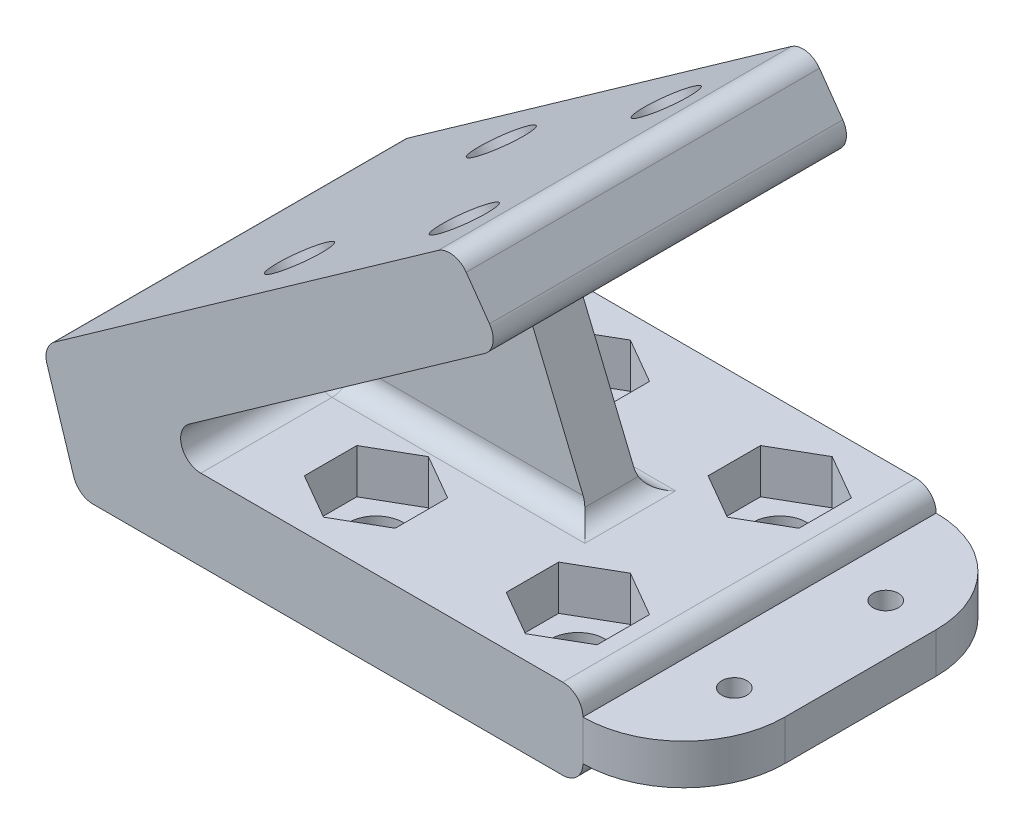
SolidWorks part; units mm, degrees
material "ABS"
ref_plane "Front Plane" through (0, 0, 0) normal (0, 0, 1) x (1, 0, 0)
ref_plane "Top Plane" through (0, 0, 0) normal (0, 1, 0) x (1, 0, 0)
ref_plane "Right Plane" through (0, 0, 0) normal (1, 0, 0) x (0, 0, -1)
sketch "Sketch1" plane through (0, 0, 0) normal (0, 0, 1) x (1, 0, 0)
  line L0 (0, 0) -> (63.5, 0)
  line L1 (63.5, 0) -> (63.5, 10.16)
  line L2 (63.5, 10.16) -> (7.4319, 10.16)
  line L3 (7.4319, 10.16) -> (53.2138, 42.5274)
  line L4 (53.2138, 42.5274) -> (47.3486, 50.8235)
  line L5 (47.3486, 50.8235) -> (-4.5018, 14.1657)
  line L6 (-4.5018, 14.1657) -> (0, 0)
  line L7 (7.4319, 10.16) -> (-2.2509, 7.0829) construction
  dimension "D1" = 35.26
  dimension "D2" = 10.16
  dimension "D3" = 63.5
  dimension "D4" = 10.16
extrude "Boss-Extrude1" add sketch "Sketch1" along normal blind 44.45 contours L0 L1 L2 L3 L4 L5 L6
sketch "Sketch2" plane through (0, 10.16, 0) normal (0, 1, 0) x (1, 0, 0)
  line L0 (27.94, -34.925) -> (53.34, -34.925) construction
  line L1 (53.34, -34.925) -> (53.34, -9.525) construction
  line L2 (53.34, -9.525) -> (27.94, -9.525) construction
  line L3 (27.94, -9.525) -> (27.94, -34.925) construction
  line L4 (40.64, -34.925) -> (40.64, -44.45) construction
  line L6 (40.64, -9.525) -> (40.64, 0) construction
  line L8 (63.5, -44.45) -> (63.5, 0) construction
  line L9 (63.5, 0) -> (7.4319, 0) construction
  line L10 (63.5, -44.45) -> (7.4319, -44.45) construction
  circle A0 centre (53.34, -34.925) radius 3.429
  circle A1 centre (53.34, -9.525) radius 3.429
  circle A2 centre (27.94, -9.525) radius 3.429
  circle A3 centre (27.94, -34.925) radius 3.429
  dimension "D2" = 6.858
  dimension "D1" = 25.4
  dimension "D3" = 10.16
extrude "Cut-Extrude1" cut sketch "Sketch2" against normal blind 44.45
sketch "Sketch3" plane through (-2.3124, 3.2708, 0) normal (0.5773, -0.8165, 0) x (0, 0, -1)
  line L0 (-34.925, 32.4418) -> (-9.525, 32.4418) construction
  line L1 (-9.525, 32.4418) -> (-9.525, 57.8418) construction
  line L2 (-9.525, 57.8418) -> (-34.925, 57.8418) construction
  line L3 (-34.925, 57.8418) -> (-34.925, 32.4418) construction
  line L4 (-44.45, 68.0018) -> (0, 68.0018) construction
  line L5 (-34.925, 45.1418) -> (-44.45, 45.1418) construction
  line L6 (-44.45, 11.9337) -> (-44.45, 68.0018) construction
  line L7 (-9.525, 45.1418) -> (0, 45.1418) construction
  line L8 (0, 11.9337) -> (0, 68.0018) construction
  circle A0 centre (-9.525, 32.4418) radius 3.429
  circle A1 centre (-9.525, 57.8418) radius 3.429
  circle A2 centre (-34.925, 57.8418) radius 3.429
  circle A3 centre (-34.925, 32.4418) radius 3.429
  dimension "D2" = 6.858
  dimension "D1" = 25.4
  dimension "D3" = 10.16
extrude "Cut-Extrude2" cut sketch "Sketch3" against normal blind 44.45
sketch "Sketch4" plane through (0, 10.16, 0) normal (0, 1, 0) x (1, 0, 0)
  line L0 (22.225, -31.6254) -> (22.225, -38.2246)
  line L1 (47.625, -31.6254) -> (47.625, -38.2246)
  line L2 (47.625, -38.2246) -> (53.34, -41.5241)
  line L3 (53.34, -41.5241) -> (59.055, -38.2246)
  line L4 (59.055, -38.2246) -> (59.055, -31.6254)
  line L5 (59.055, -31.6254) -> (53.34, -28.3259)
  line L6 (53.34, -28.3259) -> (47.625, -31.6254)
  line L7 (22.225, -38.2246) -> (27.94, -41.5241)
  line L8 (27.94, -41.5241) -> (33.655, -38.2246)
  line L9 (33.655, -38.2246) -> (33.655, -31.6254)
  line L10 (33.655, -31.6254) -> (27.94, -28.3259)
  line L11 (27.94, -28.3259) -> (22.225, -31.6254)
  line L12 (22.225, -6.2254) -> (22.225, -12.8246)
  line L13 (22.225, -12.8246) -> (27.94, -16.1241)
  line L14 (27.94, -16.1241) -> (33.655, -12.8246)
  line L15 (33.655, -12.8246) -> (33.655, -6.2254)
  line L16 (33.655, -6.2254) -> (27.94, -2.9259)
  line L17 (27.94, -2.9259) -> (22.225, -6.2254)
  line L18 (47.625, -6.2254) -> (47.625, -12.8246)
  line L19 (47.625, -12.8246) -> (53.34, -16.1241)
  line L20 (53.34, -16.1241) -> (59.055, -12.8246)
  line L21 (59.055, -12.8246) -> (59.055, -6.2254)
  line L22 (59.055, -6.2254) -> (53.34, -2.9259)
  line L23 (53.34, -2.9259) -> (47.625, -6.2254)
  circle A0 centre (53.34, -34.925) radius 5.715 construction
  circle A1 centre (27.94, -34.925) radius 5.715 construction
  circle A2 centre (27.94, -9.525) radius 5.715 construction
  circle A3 centre (53.34, -9.525) radius 5.715 construction
  circle A4 centre (53.34, -34.925) radius 3.429 construction
  dimension "D1" = 11.43
  dimension "D4" = 19.685
  dimension "D5" = 18.8009
  dimension "D2" = 2
  dimension "D3" = 2
extrude "Cut-Extrude3" cut sketch "Sketch4" against normal blind 5.588
sketch "Sketch5" plane through (-2.3124, 3.2708, 0) normal (0.5773, -0.8165, 0) x (0, 0, -1)
  line L0 (-2.9259, 57.8418) -> (-6.2254, 63.5568)
  line L1 (-28.3259, 57.8418) -> (-31.6254, 63.5568)
  line L2 (-31.6254, 63.5568) -> (-38.2246, 63.5568)
  line L3 (-38.2246, 63.5568) -> (-41.5241, 57.8418)
  line L4 (-41.5241, 57.8418) -> (-38.2246, 52.1268)
  line L5 (-38.2246, 52.1268) -> (-31.6254, 52.1268)
  line L6 (-31.6254, 52.1268) -> (-28.3259, 57.8418)
  line L7 (-6.2254, 63.5568) -> (-12.8246, 63.5568)
  line L8 (-12.8246, 63.5568) -> (-16.1241, 57.8418)
  line L9 (-16.1241, 57.8418) -> (-12.8246, 52.1268)
  line L10 (-12.8246, 52.1268) -> (-6.2254, 52.1268)
  line L11 (-6.2254, 52.1268) -> (-2.9259, 57.8418)
  line L12 (-2.9259, 32.4418) -> (-6.2254, 38.1568)
  line L13 (-6.2254, 38.1568) -> (-12.8246, 38.1568)
  line L14 (-12.8246, 38.1568) -> (-16.1241, 32.4418)
  line L15 (-16.1241, 32.4418) -> (-12.8246, 26.7268)
  line L16 (-12.8246, 26.7268) -> (-6.2254, 26.7268)
  line L17 (-6.2254, 26.7268) -> (-2.9259, 32.4418)
  line L18 (-28.3259, 32.4418) -> (-31.6254, 38.1568)
  line L19 (-31.6254, 38.1568) -> (-38.2246, 38.1568)
  line L20 (-38.2246, 38.1568) -> (-41.5241, 32.4418)
  line L21 (-41.5241, 32.4418) -> (-38.2246, 26.7268)
  line L22 (-38.2246, 26.7268) -> (-31.6254, 26.7268)
  line L23 (-31.6254, 26.7268) -> (-28.3259, 32.4418)
  circle A0 centre (-34.925, 57.8418) radius 5.715 construction
  circle A1 centre (-9.525, 57.8418) radius 5.715 construction
  circle A2 centre (-9.525, 32.4418) radius 5.715 construction
  circle A3 centre (-34.925, 32.4418) radius 5.715 construction
  circle A4 centre (-9.525, 32.4418) radius 3.429 construction
  dimension "D1" = 11.43
  dimension "D4" = 3.2996
  dimension "D5" = 5.715
  dimension "D2" = 2
  dimension "D3" = 2
extrude "Cut-Extrude4" cut sketch "Sketch5" against normal blind 5.588
ref_plane "Plane1" through (0, 0, 22.225) normal (0, 0, 1) x (1, 0, 0)
sketch "Sketch6" plane through (0, 0, 22.225) normal (0, 0, 1) x (1, 0, 0)
  line L0 (7.4319, 10.16) -> (34.3727, 37.1008)
  line L1 (34.3727, 37.1008) -> (45.5319, 10.16)
  line L2 (45.5319, 10.16) -> (7.4319, 10.16)
  dimension "D1" = 45
  dimension "D2" = 38.1
extrude "Boss-Extrude2" add sketch "Sketch6" along normal mid plane 6.35
fillet "Fillet1" radius 2.54 14 edges at (7.4319, 10.16, 9.525) (0, 0, 22.225) (-4.5018, 14.1657, 22.225) (53.2138, 42.5274, 22.225) (47.3486, 50.8235, 22.225) (63.5, 0, 22.225) (63.5, 10.16, 22.225) (26.4819, 10.16, 19.05) (22.1668, 20.5775, 19.05) (36.9018, 30.995, 22.225) (45.5319, 10.16, 22.225) (26.4819, 10.16, 25.4) (22.1668, 20.5775, 25.4) (7.4319, 10.16, 34.925)
ref_plane "Plane2" through (0, 2.54, 0) normal (0, -1, 0) x (-1, 0, 0)
sketch "Sketch7" plane through (0, 2.54, 0) normal (0, -1, 0) x (-1, 0, 0)
  line L0 (-63.5, 0) -> (-63.5, -44.45)
  line L1 (-63.5, -44.45) -> (-63.5, 0) construction
  line L2 (-76.2, -12.7) -> (-76.2, -31.75)
  line L3 (-63.5, 0) -> (-63.5, -44.45) construction
  line L4 (-63.5, 0) -> (0, 0) construction
  line L5 (-69.85, -1.7015) -> (-69.85, -42.7485) construction
  line L6 (-69.85, -1.7015) -> (-69.85, -12.7) construction
  line L7 (-69.85, -12.7) -> (-69.85, -31.75) construction
  line L8 (-69.85, -31.75) -> (-69.85, -42.7485) construction
  arc A0 (-76.2, -31.75) -> (-63.5, -44.45) centre (-63.5, -31.75) ccw
  arc A1 (-76.2, -12.7) -> (-63.5, 0) centre (-63.5, -12.7) cw
  circle A2 centre (-69.85, -12.7) radius 1.5875
  circle A3 centre (-69.85, -31.75) radius 1.5875
  dimension "D3" = 3.175
  dimension "D1" = 12.7
  dimension "D2" = 6.35
  dimension "D4" = 19.05
extrude "Boss-Extrude3" add sketch "Sketch7" against normal up to vertex (5.08 mm away) up to point (63.5, 7.62, 0)
